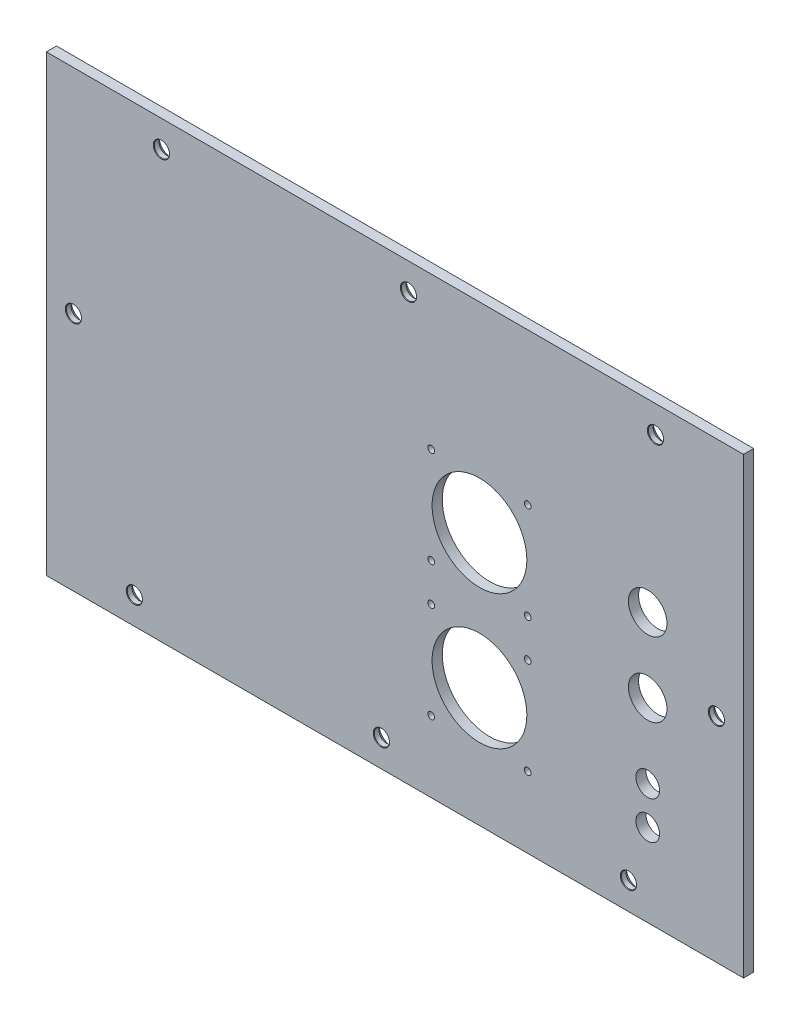
SolidWorks part; units mm, degrees
ref_plane "Спереди" through (0, 0, 0) normal (0, 0, 1) x (1, 0, 0)
ref_plane "Сверху" through (0, 0, 0) normal (0, 1, 0) x (1, 0, 0)
ref_plane "Справа" through (0, 0, 0) normal (1, 0, 0) x (0, 0, -1)
sketch "Эскиз1" plane through (0, 0, 0) normal (0, 0, 1) x (1, 0, 0)
  line L1 (0, 0) -> (206, 0)
  line L2 (0, 0) -> (0, 134)
  line L3 (0, 134) -> (206, 134)
  line L4 (206, 0) -> (206, 134)
  line L5 (113.7333, 60.6896) -> (142.2333, 60.6896) construction
  line L6 (113.7333, 60.6896) -> (113.7333, 89.1896) construction
  line L7 (113.7333, 89.1896) -> (142.2333, 89.1896) construction
  line L8 (142.2333, 60.6896) -> (142.2333, 89.1896) construction
  line L9 (113.7333, 60.6896) -> (142.2333, 89.1896) construction
  line L10 (113.7333, 89.1896) -> (142.2333, 60.6896) construction
  line L11 (113.7333, 20.9998) -> (142.2333, 20.9998) construction
  line L12 (113.7333, 20.9998) -> (113.7333, 49.4998) construction
  line L13 (113.7333, 49.4998) -> (142.2333, 49.4998) construction
  line L14 (142.2333, 20.9998) -> (142.2333, 49.4998) construction
  line L15 (113.7333, 20.9998) -> (142.2333, 49.4998) construction
  line L16 (113.7333, 49.4998) -> (142.2333, 20.9998) construction
  circle A0 centre (127.9833, 74.9396) radius 14
  circle A1 centre (127.9833, 35.2498) radius 14
  circle A2 centre (177.6911, 35.5606) radius 3.5
  circle A3 centre (177.6911, 24.371) radius 3.5
  circle A4 centre (177.6911, 79.4346) radius 5.7
  circle A5 centre (177.6911, 57.5096) radius 5.7
  circle A6 centre (113.7333, 89.1896) radius 1
  circle A7 centre (142.2333, 89.1896) radius 1
  circle A8 centre (113.7333, 49.4998) radius 1
  circle A9 centre (142.2333, 49.4998) radius 1
  circle A10 centre (142.2333, 20.9998) radius 1
  circle A11 centre (113.7333, 20.9998) radius 1
  circle A12 centre (142.2333, 60.6896) radius 1
  circle A13 centre (113.7333, 60.6896) radius 1
  dimension "D3" = 28
  dimension "D4" = 11.4
  dimension "D5" = 7
  dimension "D7" = 2
  dimension "D1" = 134
  dimension "D2" = 206
  dimension "D6" = 28.5
extrude "Бобышка-Вытянуть1" add sketch "Эскиз1" along normal blind 3
hole_wizard "Зенковка для винта с потайной головкой M41" positions "Эскиз3" profile "Эскиз2" countersink size "M4" standard "DIN" end condition through all
sketch "Эскиз3" plane through (0, 0, 0) normal (0, 0, -1) x (-1, 0, 0)
  line L0 (0, 134) -> (0, 0) construction
  line L1 (0, 0) -> (-206, 0) construction
  line L2 (-206, 134) -> (0, 134) construction
  line L3 (-206, 0) -> (-206, 134) construction
  point P1 (-26, 8)
  point P3 (-99, 8)
  point P5 (-172, 8)
  point P7 (-198, 63)
  point P9 (-180, 126)
  point P11 (-107, 126)
  point P13 (-34, 126)
  point P15 (-8, 71)
  dimension "D1" = 73
  dimension "D2" = 73
  dimension "D3" = 73
  dimension "D4" = 73
  dimension "D5" = 26
  dimension "D6" = 8
  dimension "D7" = 63
  dimension "D8" = 8
  dimension "D9" = 63
  dimension "D10" = 26
  dimension "D11" = 8
sketch "Эскиз2" plane through (26, 8, 0) normal (1, 0, 0) x (0, 1, 0)
  line L0 (0, 0) -> (0, 3)
  line L1 (0, 3) -> (2.4, 3)
  line L2 (2.25, 2.85) -> (2.25, 1.45)
  line L3 (2.25, 1.45) -> (3.7, 0)
  line L5 (3.7, 0) -> (0, 0)
  line L6 (-2.25, 1.45) -> (-3.7, 0) construction
  line L7 (2.4, 3) -> (2.25, 2.85)
  line L8 (-2.4, 3) -> (-2.25, 2.85) construction
  line L11 (0, -6.35) -> (0, 107.95) construction
  dimension "Диаметр сквозного отверстия" = 4.5
  dimension "Глубина сквозного отверстия" = 3
  dimension "Диаметр передней зенковки" = 7.4
  dimension "Угол передней зенковки" = 90
  dimension "Диаметр задней зенковки" = 4.8
  dimension "Угол задней зенковки" = 90
